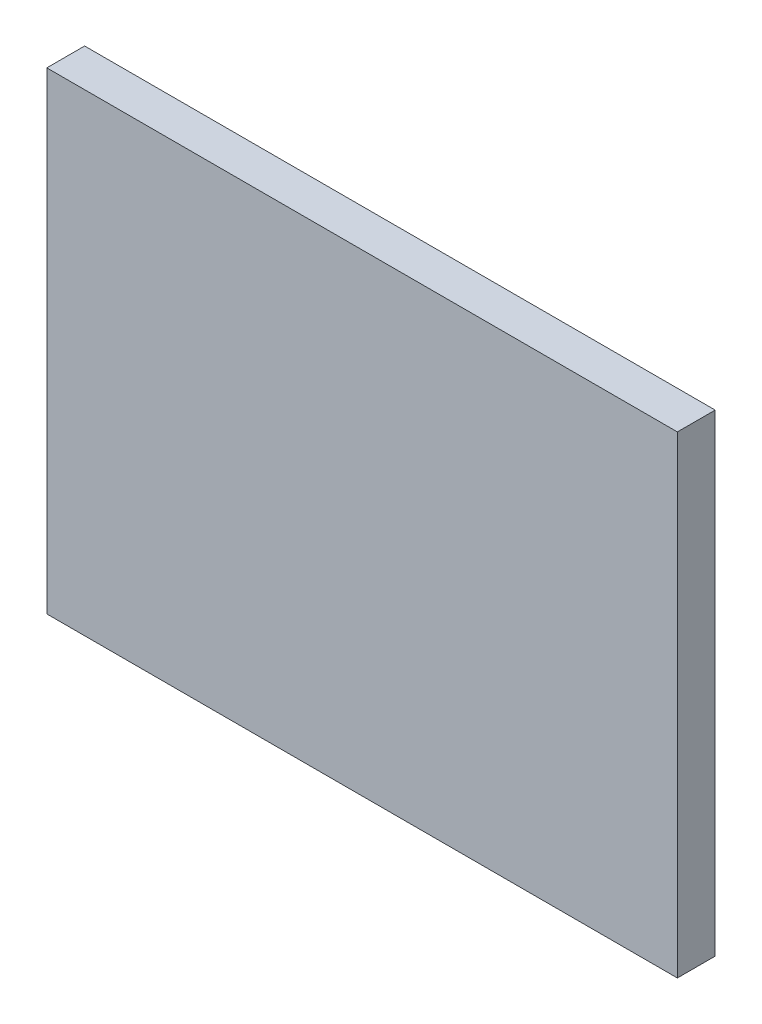
SolidWorks part; units mm, degrees
material "Vidro"
ref_plane "Plano frontal" through (0, 0, 0) normal (0, 0, 1) x (1, 0, 0)
ref_plane "Plano superior" through (0, 0, 0) normal (0, 1, 0) x (1, 0, 0)
ref_plane "Plano direito" through (0, 0, 0) normal (1, 0, 0) x (0, 0, -1)
sketch "Esboço1" plane through (0, 0, 0) normal (0, 0, 1) x (1, 0, 0)
  line L1 (0, 0) -> (-20, 0)
  line L2 (0, 0) -> (0, 15)
  line L3 (0, 15) -> (-20, 15)
  line L4 (-20, 0) -> (-20, 15)
extrude "Ressalto-extrusão1" add sketch "Esboço1" along normal blind 1.2
